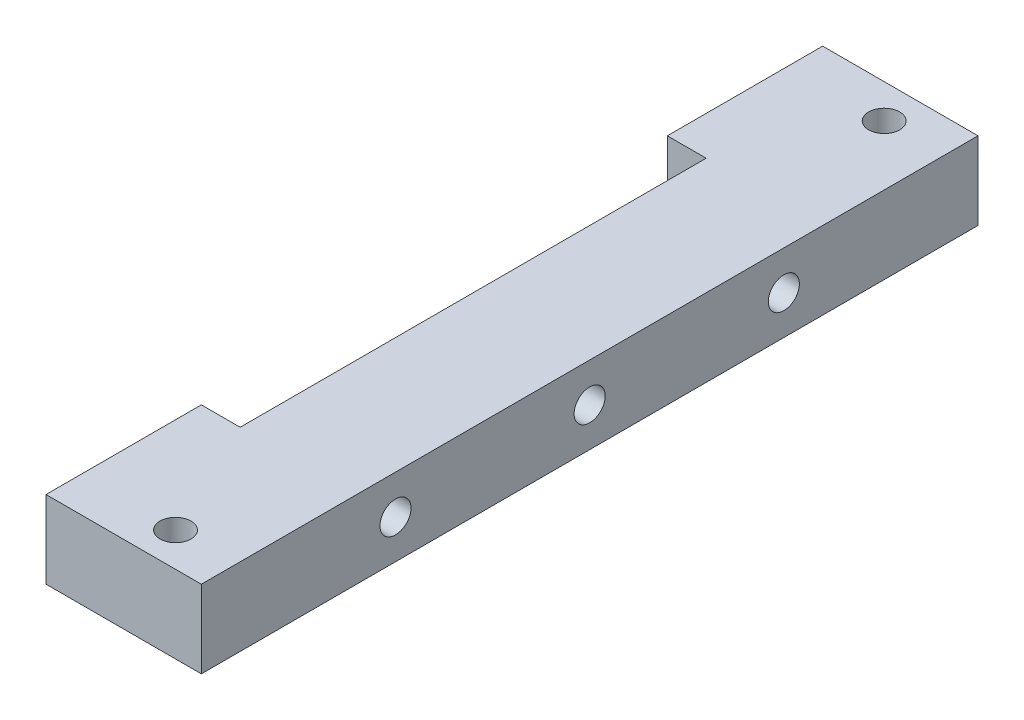
SolidWorks part; units mm, degrees
ref_plane "Front Plane" through (0, 0, 0) normal (0, 0, 1) x (1, 0, 0)
ref_plane "Top Plane" through (0, 0, 0) normal (0, 1, 0) x (1, 0, 0)
ref_plane "Right Plane" through (0, 0, 0) normal (1, 0, 0) x (0, 0, -1)
sketch "Sketch1" plane through (0, 0, 0) normal (0, 1, 0) x (1, 0, 0)
  line L0 (16.0507, 56.815) -> (-8.9493, 56.815)
  line L1 (1.0507, -23.185) -> (1.0507, 36.815)
  line L2 (16.0507, -43.185) -> (16.0507, 56.815)
  line L3 (-8.9493, 56.815) -> (-8.9493, 36.815)
  line L4 (-8.9493, -43.185) -> (-8.9493, -23.185)
  line L5 (16.0507, -43.185) -> (-8.9493, -43.185)
  line L6 (-8.9493, -23.185) -> (1.0507, -23.185)
  line L7 (-8.9493, 36.815) -> (1.0507, 36.815)
  circle A0 centre (8.3489, 52.4361) radius 2
  circle A1 centre (8.3489, -38.8061) radius 2
extrude "Boss-Extrude1" add sketch "Sketch1" along normal blind 10
sketch "Sketch2" plane through (1.0507, 0, 0) normal (-1, 0, 0) x (0, 0, 1)
  line L3 (-36.815, 10) -> (23.185, 10)
  line L5 (-36.815, 10) -> (-36.815, 0)
  line L6 (-36.815, 0) -> (23.185, 0)
  line L7 (23.185, 10) -> (23.185, 0)
  circle A0 centre (-31.815, 5) radius 2
  circle A1 centre (18.185, 5) radius 2
  circle A2 centre (-6.815, 5) radius 2
extrude "Cut-Extrude1" cut sketch "Sketch2" against normal blind 30 contours A0 | A2 | A1
sketch "Sketch3" plane through (-8.9493, 0, 0) normal (-1, 0, 0) x (0, 0, 1)
  line L1 (-82.0066, 38.4892) -> (65.0659, 38.4892)
  line L2 (-82.0066, 38.4892) -> (-82.0066, -22.8865)
  line L3 (-82.0066, -22.8865) -> (65.0659, -22.8865)
  line L4 (65.0659, 38.4892) -> (65.0659, -22.8865)
extrude "Cut-Extrude2" cut sketch "Sketch3" against normal offset from surface (5 mm away) 5 up to face at (1.0507, 5, -4.815)
